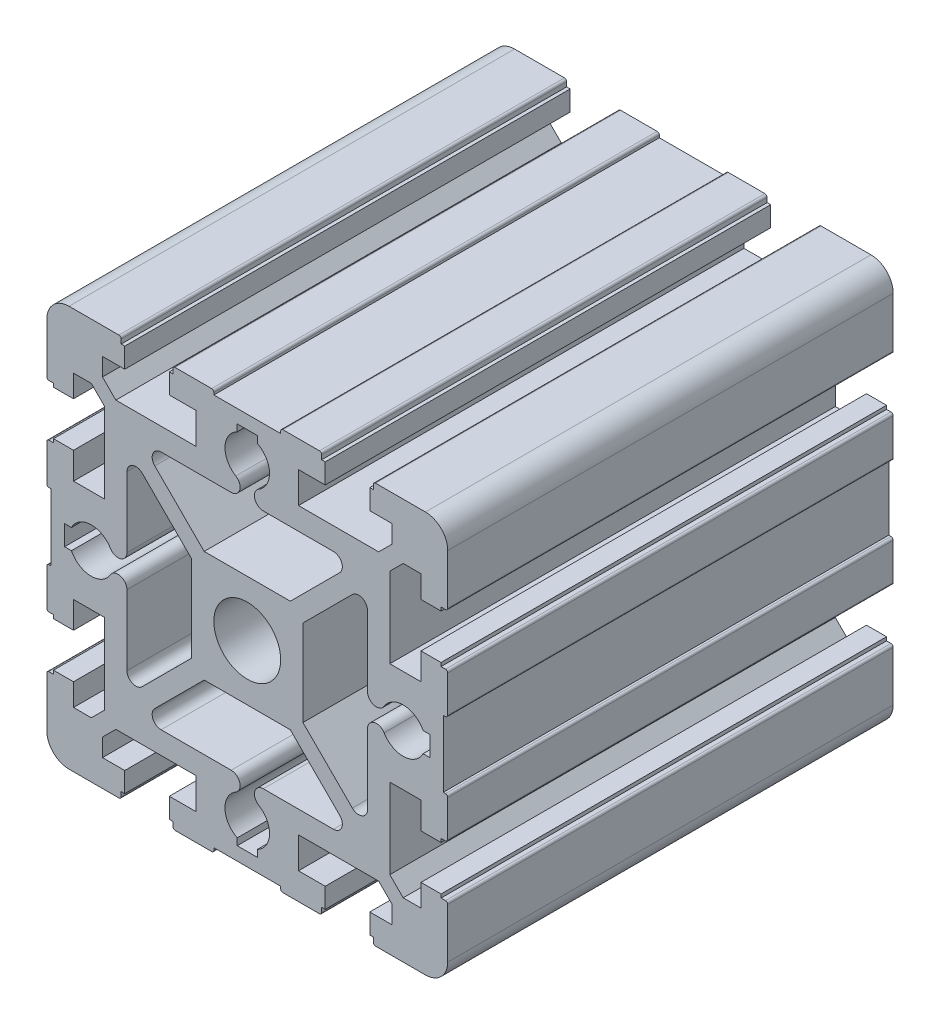
SolidWorks part; units mm, degrees
material "АД31 ГОСТ 4784-97"
ref_plane "Front Plane" through (0, 0, 0) normal (0, 0, 1) x (1, 0, 0)
ref_plane "Top Plane" through (0, 0, 0) normal (0, 1, 0) x (1, 0, 0)
ref_plane "Right Plane" through (0, 0, 0) normal (1, 0, 0) x (0, 0, -1)
sketch "Sketch1" plane through (0, 0, 0) normal (0, 0, 1) x (1, 0, 0)
  line L0 (12.5, -9.6715) -> (23.5857, -20.7573)
  line L1 (27, -19.3431) -> (27, -3.6055)
  line L2 (39.4651, -2.25) -> (40.9999, -2.25)
  line L3 (40.9999, -2.25) -> (40.9999, 2.25)
  line L4 (40.9999, 2.25) -> (39.4651, 2.25)
  line L5 (27, 3.6055) -> (27, 19.3431)
  line L6 (23.5857, 20.7573) -> (12.5, 9.6716)
  line L7 (12.5, 9.6716) -> (12.5, -9.6715)
  line L8 (16.6999, -44.5) -> (16.6999, -43.5)
  line L9 (7.9999, -45) -> (16.1999, -45)
  line L10 (7.4999, -44.5) -> (7.4999, -44)
  line L11 (7.4999, -44) -> (-7.5001, -44)
  line L12 (-7.5001, -44) -> (-7.5001, -44.5)
  line L13 (-16.2001, -45) -> (-8.0001, -45)
  line L14 (-16.7001, -44.5) -> (-16.7001, -43.5)
  line L15 (-16.7001, -43.5) -> (-17.5001, -43.5)
  line L16 (-17.5001, -43.5) -> (-17.5001, -39)
  line L17 (-17.5001, -39) -> (-11.5001, -39)
  line L18 (-11.5001, -39) -> (-11.5001, -32)
  line L19 (-11.5001, -32) -> (-29.5, -32)
  line L20 (-29.5, -32) -> (-32.5, -35)
  line L21 (-32.5, -35) -> (-32.5, -39)
  line L22 (-32.5, -39) -> (-27.5, -39)
  line L23 (-27.5, -39) -> (-27.5, -43.5)
  line L24 (-27.5, -43.5) -> (-28.3, -43.5)
  line L25 (-28.3, -43.5) -> (-28.3, -44.5)
  line L26 (-40, -45) -> (-28.8, -45)
  line L27 (-45, -40) -> (-45, -28.7999)
  line L28 (-44.5, -28.2999) -> (-43.5, -28.2999)
  line L29 (-43.5, -28.2999) -> (-43.5, -27.4999)
  line L30 (-43.5, -27.4999) -> (-39, -27.4999)
  line L31 (-39, -27.4999) -> (-39, -32.4999)
  line L32 (-39, -32.4999) -> (-35, -32.4999)
  line L33 (-35, -32.4999) -> (-32, -29.4999)
  line L34 (-32, -29.4999) -> (-32, -11.5)
  line L35 (-32, -11.5) -> (-39, -11.5)
  line L36 (-39, -11.5) -> (-39, -17.5)
  line L37 (-39, -17.5) -> (-43.5, -17.5)
  line L38 (-43.5, -17.5) -> (-43.5, -16.7)
  line L39 (-43.5, -16.7) -> (-44.5, -16.7)
  line L40 (-45, -16.2) -> (-45, -8)
  line L41 (-44.5, -7.5) -> (-44, -7.5)
  line L42 (-44, -7.5) -> (-44, 7.5)
  line L43 (-44, 7.5) -> (-44.5, 7.5)
  line L44 (-45, 8) -> (-45, 16.2)
  line L45 (-44.5, 16.7) -> (-43.5, 16.7)
  line L46 (-43.5, 16.7) -> (-43.5, 17.5)
  line L47 (-43.5, 17.5) -> (-39, 17.5)
  line L48 (-39, 17.5) -> (-39, 11.5)
  line L49 (-39, 11.5) -> (-32, 11.5)
  line L50 (-32, 11.5) -> (-32, 29.4999)
  line L51 (-32, 29.4999) -> (-35, 32.4999)
  line L52 (-35, 32.4999) -> (-39, 32.4999)
  line L53 (-39, 32.4999) -> (-39, 27.4999)
  line L54 (-39, 27.4999) -> (-43.5, 27.4999)
  line L55 (-43.5, 27.4999) -> (-43.5, 28.2999)
  line L56 (-43.5, 28.2999) -> (-44.5, 28.2999)
  line L57 (-45, 28.7999) -> (-45, 40)
  line L58 (-40, 45) -> (-28.8, 45)
  line L59 (-28.3, 44.5) -> (-28.3, 43.5)
  line L60 (-28.3, 43.5) -> (-27.5, 43.5)
  line L61 (-27.5, 43.5) -> (-27.5, 39)
  line L62 (-27.5, 39) -> (-32.5, 39)
  line L63 (-32.5, 39) -> (-32.5, 35)
  line L64 (-32.5, 35) -> (-29.5, 32)
  line L65 (-29.5, 32) -> (-11.5001, 32)
  line L66 (-11.5001, 32) -> (-11.5001, 39)
  line L67 (-11.5001, 39) -> (-17.5, 39)
  line L68 (-17.5, 39) -> (-17.5, 43.5)
  line L69 (-17.5, 43.5) -> (-16.7, 43.5)
  line L70 (-16.7, 43.5) -> (-16.7, 44.5)
  line L71 (-16.2, 45) -> (-8.0001, 45)
  line L72 (-7.5001, 44.5) -> (-7.5001, 44)
  line L73 (-7.5001, 44) -> (7.4999, 44)
  line L74 (7.4999, 44) -> (7.4999, 44.5)
  line L75 (7.9999, 45) -> (16.1999, 45)
  line L76 (16.6999, 44.5) -> (16.6999, 43.5)
  line L77 (16.6999, 43.5) -> (17.4999, 43.5)
  line L78 (17.4999, 43.5) -> (17.4999, 39)
  line L79 (17.4999, 39) -> (11.4999, 39)
  line L80 (11.4999, 39) -> (11.4999, 32)
  line L81 (11.4999, 32) -> (29.4999, 32)
  line L82 (29.4999, 32) -> (32.4999, 35)
  line L83 (32.4999, 35) -> (32.4999, 39)
  line L84 (32.4999, 39) -> (27.5, 39)
  line L85 (27.5, 39) -> (27.5, 43.5)
  line L86 (27.5, 43.5) -> (28.3, 43.5)
  line L87 (28.3, 43.5) -> (28.3, 44.5)
  line L88 (28.8, 45) -> (40, 45)
  line L89 (45, 28.7999) -> (45, 40)
  line L90 (44.5, 28.2999) -> (43.5, 28.2999)
  line L91 (43.5, 28.2999) -> (43.5, 27.4999)
  line L92 (43.5, 27.4999) -> (39, 27.4999)
  line L93 (39, 27.4999) -> (39, 32.4999)
  line L94 (39, 32.4999) -> (35, 32.4999)
  line L95 (35, 32.4999) -> (32, 29.4999)
  line L96 (32, 29.4999) -> (32, 11.5)
  line L97 (32, 11.5) -> (39, 11.5)
  line L98 (39, 11.5) -> (39, 17.5)
  line L99 (39, 17.5) -> (43.5, 17.5)
  line L100 (43.5, 17.5) -> (43.5, 16.7)
  line L101 (43.5, 16.7) -> (44.5, 16.7)
  line L102 (45, 8) -> (45, 16.2)
  line L103 (44.5, 7.5) -> (44, 7.5)
  line L104 (44, 7.5) -> (44, -7.5)
  line L105 (44, -7.5) -> (44.5, -7.5)
  line L106 (45, -16.2) -> (45, -8)
  line L107 (44.5, -16.7) -> (43.5, -16.7)
  line L108 (43.5, -16.7) -> (43.5, -17.5)
  line L109 (43.5, -17.5) -> (39, -17.5)
  line L110 (39, -17.5) -> (39, -11.5)
  line L111 (39, -11.5) -> (32, -11.5)
  line L112 (32, -11.5) -> (32, -29.4999)
  line L113 (32, -29.4999) -> (35, -32.4999)
  line L114 (35, -32.4999) -> (39, -32.4999)
  line L115 (39, -32.4999) -> (39, -27.4999)
  line L116 (39, -27.4999) -> (43.5, -27.4999)
  line L117 (43.5, -27.4999) -> (43.5, -28.2999)
  line L118 (43.5, -28.2999) -> (44.5, -28.2999)
  line L119 (45, -40) -> (45, -28.7999)
  line L120 (28.8, -45) -> (40, -45)
  line L121 (28.3, -44.5) -> (28.3, -43.5)
  line L122 (28.3, -43.5) -> (27.5, -43.5)
  line L123 (27.5, -43.5) -> (27.5, -39)
  line L124 (27.5, -39) -> (32.4998, -39)
  line L125 (32.4998, -39) -> (32.4998, -35)
  line L126 (32.4998, -35) -> (29.4999, -32)
  line L127 (29.4999, -32) -> (11.4999, -32)
  line L128 (11.4999, -32) -> (11.4999, -39)
  line L129 (11.4999, -39) -> (17.4999, -39)
  line L130 (17.4999, -39) -> (17.4999, -43.5)
  line L131 (17.4999, -43.5) -> (16.6999, -43.5)
  line L132 (-20.7573, -23.5857) -> (-9.6716, -12.5)
  line L133 (-19.3431, -26.9999) -> (-3.6055, -26.9999)
  line L134 (-2.25, -39.4651) -> (-2.25, -40.9999)
  line L135 (-2.25, -40.9999) -> (2.25, -40.9999)
  line L136 (2.25, -40.9999) -> (2.25, -39.4651)
  line L137 (3.6056, -26.9999) -> (19.3431, -26.9999)
  line L138 (20.7573, -23.5857) -> (9.6716, -12.5)
  line L139 (9.6716, -12.5) -> (-9.6716, -12.5)
  line L140 (9.6715, 12.5) -> (20.7573, 23.5857)
  line L141 (3.6056, 26.9999) -> (19.3431, 26.9999)
  line L142 (2.25, 39.4651) -> (2.25, 40.9999)
  line L143 (2.25, 40.9999) -> (-2.25, 40.9999)
  line L144 (-2.25, 40.9999) -> (-2.25, 39.4651)
  line L145 (-19.3431, 26.9999) -> (-3.6056, 26.9999)
  line L146 (-20.7573, 23.5857) -> (-9.6716, 12.5)
  line L147 (-9.6716, 12.5) -> (9.6715, 12.5)
  line L148 (0, 54.4017) -> (0, -48.5613) construction
  line L149 (-12.5, -9.6715) -> (-23.5857, -20.7573)
  line L150 (-27, -19.3431) -> (-27, -3.6055)
  line L151 (-40.9999, 2.25) -> (-39.4651, 2.25)
  line L152 (-40.9999, -2.25) -> (-40.9999, 2.25)
  line L153 (-39.4651, -2.25) -> (-40.9999, -2.25)
  line L154 (-27, 3.6055) -> (-27, 19.3431)
  line L155 (-23.5857, 20.7573) -> (-12.5, 9.6716)
  line L156 (-12.5, 9.6716) -> (-12.5, -9.6715)
  line L157 (-49.3461, 0) -> (51.259, 0) construction
  line L159 (41.25, 22.5) -> (61.1063, 22.5) construction
  line L161 (41.25, -22.5) -> (59.933, -22.5) construction
  arc A0 (-23.5857, -20.7573) -> (-27, -19.3431) centre (-25, -19.3431) cw
  arc A1 (-39.4651, 2.25) -> (-30.7142, 2.5754) centre (-34.9999, 0) cw
  arc A2 (-30.7142, -2.5754) -> (-39.4651, -2.25) centre (-34.9999, 0) cw
  arc A3 (-30.7142, -2.5754) -> (-27, -3.6055) centre (-29, -3.6055) cw
  arc A4 (-27, 3.6055) -> (-30.7142, 2.5754) centre (-29, 3.6055) cw
  arc A5 (-27, 19.3431) -> (-23.5857, 20.7573) centre (-25, 19.3431) cw
  arc A6 (23.5857, -20.7573) -> (27, -19.3431) centre (25, -19.3431) ccw
  arc A7 (30.7142, -2.5754) -> (27, -3.6055) centre (29, -3.6055) ccw
  arc A8 (30.7142, -2.5754) -> (39.4651, -2.25) centre (34.9999, 0) ccw
  arc A9 (39.4651, 2.25) -> (30.7142, 2.5754) centre (34.9999, 0) ccw
  arc A10 (27, 3.6055) -> (30.7142, 2.5754) centre (29, 3.6055) ccw
  arc A11 (27, 19.3431) -> (23.5857, 20.7573) centre (25, 19.3431) ccw
  circle A12 centre (0, 0) radius 7.5
  arc A13 (16.1999, -45) -> (16.6999, -44.5) centre (16.1999, -44.5) ccw
  arc A14 (7.4999, -44.5) -> (7.9999, -45) centre (7.9999, -44.5) ccw
  arc A15 (-8.0001, -45) -> (-7.5001, -44.5) centre (-8.0001, -44.5) ccw
  arc A16 (-16.7001, -44.5) -> (-16.2001, -45) centre (-16.2001, -44.5) ccw
  arc A17 (-28.8, -45) -> (-28.3, -44.5) centre (-28.8, -44.5) ccw
  arc A18 (-45, -40) -> (-40, -45) centre (-40, -40) ccw
  arc A19 (-44.5, -28.2999) -> (-45, -28.7999) centre (-44.5, -28.7999) ccw
  arc A20 (-45, -16.2) -> (-44.5, -16.7) centre (-44.5, -16.2) ccw
  arc A21 (-44.5, -7.5) -> (-45, -8) centre (-44.5, -8) ccw
  arc A22 (-45, 8) -> (-44.5, 7.5) centre (-44.5, 8) ccw
  arc A23 (-44.5, 16.7) -> (-45, 16.2) centre (-44.5, 16.2) ccw
  arc A24 (-45, 28.7999) -> (-44.5, 28.2999) centre (-44.5, 28.7999) ccw
  arc A25 (-40, 45) -> (-45, 40) centre (-40, 40) ccw
  arc A26 (-28.3, 44.5) -> (-28.8, 45) centre (-28.8, 44.5) ccw
  arc A27 (-16.2, 45) -> (-16.7, 44.5) centre (-16.2, 44.5) ccw
  arc A28 (-7.5001, 44.5) -> (-8.0001, 45) centre (-8.0001, 44.5) ccw
  arc A29 (7.9999, 45) -> (7.4999, 44.5) centre (7.9999, 44.5) ccw
  arc A30 (16.6999, 44.5) -> (16.1999, 45) centre (16.1999, 44.5) ccw
  arc A31 (28.8, 45) -> (28.3, 44.5) centre (28.8, 44.5) ccw
  arc A32 (45, 40) -> (40, 45) centre (40, 40) ccw
  arc A33 (44.5, 28.2999) -> (45, 28.7999) centre (44.5, 28.7999) ccw
  arc A34 (45, 16.2) -> (44.5, 16.7) centre (44.5, 16.2) ccw
  arc A35 (44.5, 7.5) -> (45, 8) centre (44.5, 8) ccw
  arc A36 (45, -8) -> (44.5, -7.5) centre (44.5, -8) ccw
  arc A37 (44.5, -16.7) -> (45, -16.2) centre (44.5, -16.2) ccw
  arc A38 (45, -28.7999) -> (44.5, -28.2999) centre (44.5, -28.7999) ccw
  arc A39 (40, -45) -> (45, -40) centre (40, -40) ccw
  arc A40 (28.3, -44.5) -> (28.8, -45) centre (28.8, -44.5) ccw
  arc A41 (-20.7573, -23.5857) -> (-19.3431, -26.9999) centre (-19.3431, -25) ccw
  arc A42 (-2.5754, -30.7142) -> (-3.6055, -26.9999) centre (-3.6055, -28.9999) ccw
  arc A43 (-2.5754, -30.7142) -> (-2.25, -39.4651) centre (0, -34.9999) ccw
  arc A44 (2.25, -39.4651) -> (2.5754, -30.7142) centre (0, -34.9999) ccw
  arc A45 (3.6056, -26.9999) -> (2.5754, -30.7142) centre (3.6056, -28.9999) ccw
  arc A46 (19.3431, -26.9999) -> (20.7573, -23.5857) centre (19.3431, -25) ccw
  arc A47 (20.7573, 23.5857) -> (19.3431, 26.9999) centre (19.3431, 24.9999) ccw
  arc A48 (2.5754, 30.7142) -> (3.6056, 26.9999) centre (3.6056, 28.9999) ccw
  arc A49 (2.5754, 30.7142) -> (2.25, 39.4651) centre (0, 34.9999) ccw
  arc A50 (-2.25, 39.4651) -> (-2.5754, 30.7142) centre (0, 34.9999) ccw
  arc A51 (-3.6056, 26.9999) -> (-2.5754, 30.7142) centre (-3.6056, 28.9999) ccw
  arc A52 (-19.3431, 26.9999) -> (-20.7573, 23.5857) centre (-19.3431, 25) ccw
  dimension "D2" = 10
  dimension "D4" = 15
  dimension "D1" = 90
  dimension "D3" = 45
  dimension "D5" = 13
  dimension "D6" = 22.5
  dimension "D7" = 10
  dimension "D8" = 90
extrude "Base-Extrude" add sketch "Sketch1" against normal blind 100
sketch "Sketch18" plane through (0, 0, 0) normal (0, 1, 0) x (1, 0, 0)
  line L0 (-68.7285, 45) -> (85.0543, 45) construction
  line L1 (45, 60.5) -> (45, 45)
  line L2 (45, 45) -> (-45, 45)
  line L3 (15.3047, 60.5) -> (45, 60.5)
  line L4 (15.3047, 60.5) -> (12, 55)
  line L5 (12, 55) -> (-45, 55)
  line L6 (-45, 55) -> (-45, 45)
  line L7 (40, 0) -> (28.8, 0) construction
  line L8 (-45, 100) -> (-45, 0) construction
  line L9 (45, 100) -> (45, 0) construction
  dimension "D1" = 45
  dimension "Countersunk Dia" = 31
  dimension "Thru Hole Dia" = 20
  dimension "D4" = 33
  dimension "D5" = 59
